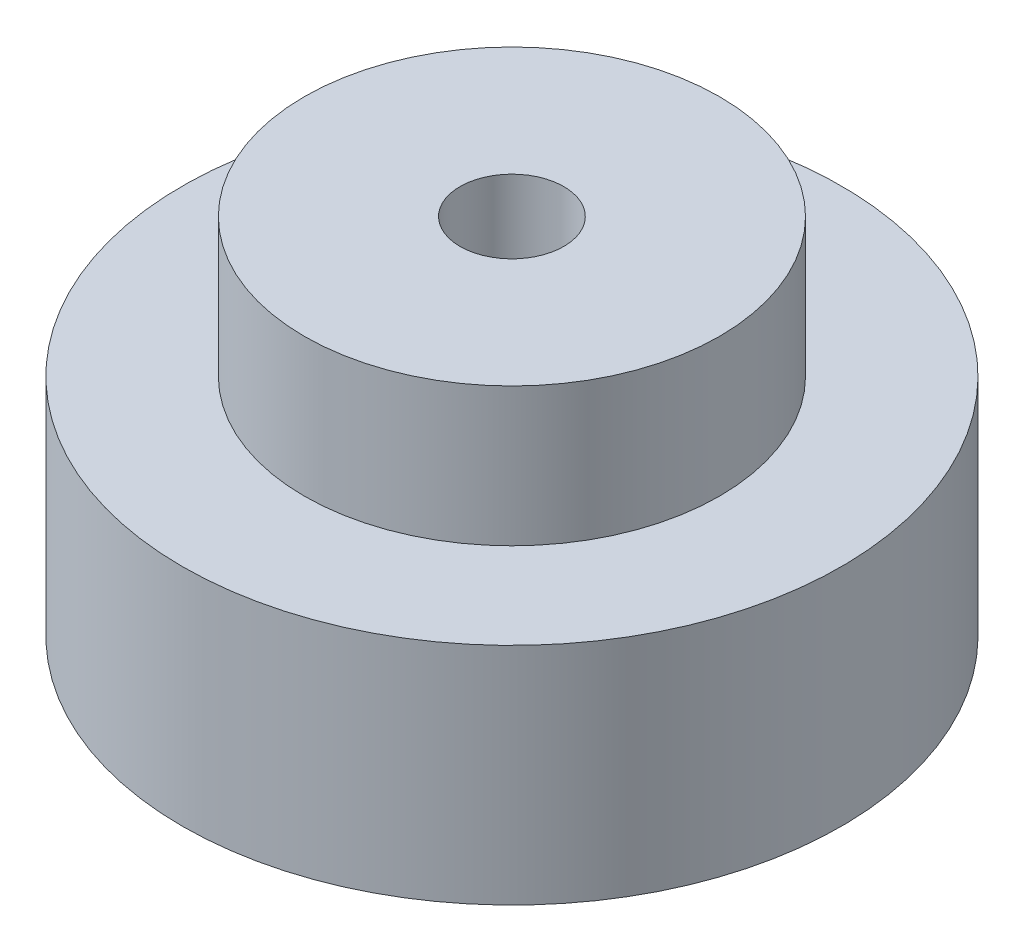
SolidWorks part; units mm, degrees
material "Rubber"
ref_plane "Front Plane" through (0, 0, 0) normal (0, 0, 1) x (1, 0, 0)
ref_plane "Top Plane" through (0, 0, 0) normal (0, 1, 0) x (1, 0, 0)
ref_plane "Right Plane" through (0, 0, 0) normal (1, 0, 0) x (0, 0, -1)
sketch "Sketch1" plane through (0, 0, 0) normal (0, 1, 0) x (1, 0, 0)
  circle A0 centre (0, 0) radius 19.05
  circle A1 centre (0, 0) radius 3
  dimension "D1" = 38.1
  dimension "D2" = 6
extrude "Boss-Extrude1" add sketch "Sketch1" along normal blind 13
sketch "Sketch2" plane through (0, 13, 0) normal (0, 1, 0) x (1, 0, 0)
  circle A0 centre (0, 0) radius 3
  circle A1 centre (0, 0) radius 12
  dimension "D1" = 24
extrude "Boss-Extrude2" add sketch "Sketch2" along normal blind 8
